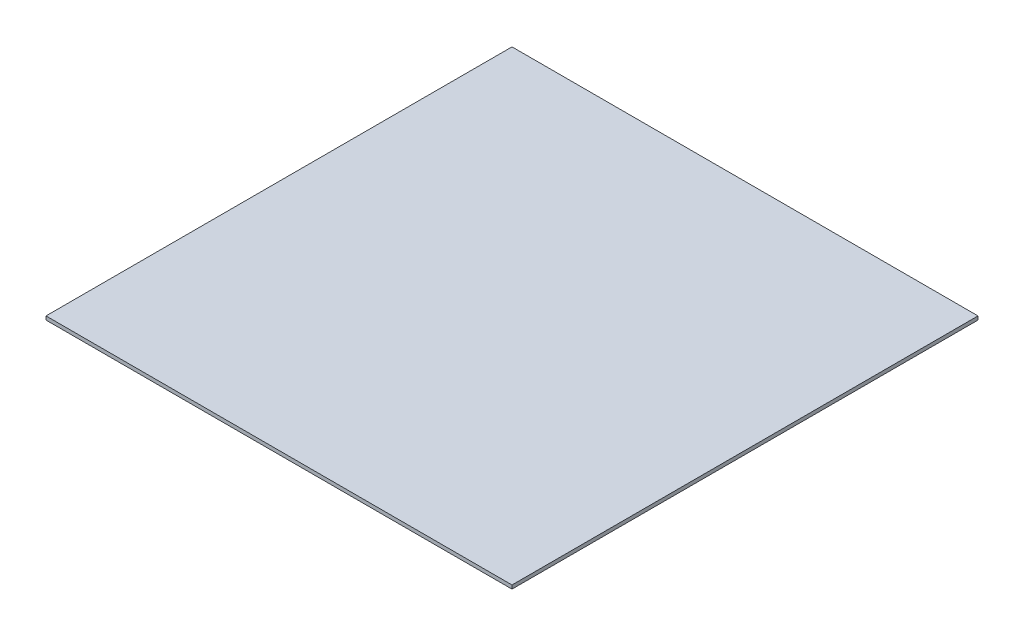
SolidWorks part; units mm, degrees
ref_plane "Front Plane" through (0, 0, 0) normal (0, 0, 1) x (1, 0, 0)
ref_plane "Top Plane" through (0, 0, 0) normal (0, 1, 0) x (1, 0, 0)
ref_plane "Right Plane" through (0, 0, 0) normal (1, 0, 0) x (0, 0, -1)
sketch "Sketch1" plane through (0, 0, 0) normal (0, 1, 0) x (1, 0, 0)
  line L1 (640.6387, 640.6387) -> (-640.6387, 640.6387)
  line L2 (-640.6387, 640.6387) -> (-640.6387, -640.6387)
  line L3 (-640.6387, -640.6387) -> (640.6387, -640.6387)
  line L4 (640.6387, -640.6387) -> (640.6387, 640.6387)
  circle A0 centre (0, 0) radius 906 construction
extrude "Boss-Extrude1" add sketch "Sketch1" along normal blind 10
